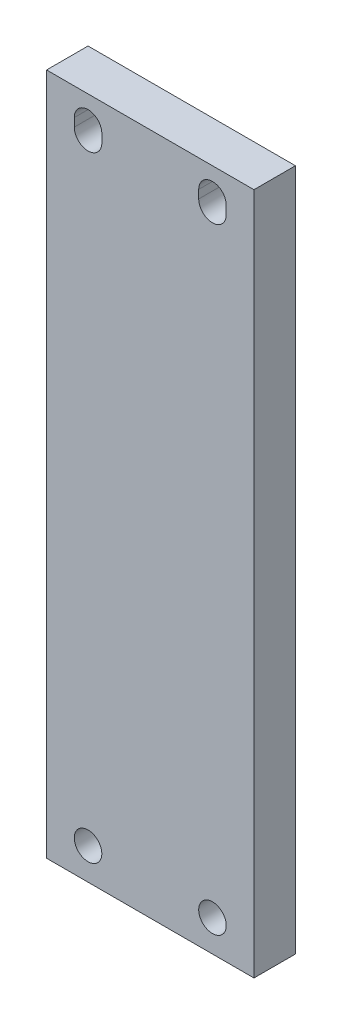
SolidWorks part; units mm, degrees
material "6061-T6 Al"
ref_plane "Front" through (0, 0, 0) normal (0, 0, 1) x (1, 0, 0)
ref_plane "Top" through (0, 0, 0) normal (0, 1, 0) x (1, 0, 0)
ref_plane "Right" through (0, 0, 0) normal (1, 0, 0) x (0, 0, -1)
sketch "Sketch1 w/mock PCB" plane through (0, 0, 0) normal (0, 0, 1) x (1, 0, 0)
  line L0 (-31.75, 104.521) -> (31.75, -104.521) construction
  line L2 (-31.75, 104.521) -> (31.75, 104.521)
  line L3 (-31.75, 104.521) -> (-31.75, -104.521)
  line L4 (-31.75, -104.521) -> (31.75, -104.521)
  line L6 (31.75, 104.521) -> (31.75, -104.521)
  point P5 (-25.908, 20.828)
  point P6 (25.908, 20.828)
  point P7 (25.908, -20.828)
  point P8 (-25.908, -20.828)
  point P63 (-25.781, -19.05)
  point P64 (25.781, -19.05)
  dimension "D1" = 63.5
  dimension "D2" = 209.042
extrude "Boss-Extrude1" add sketch "Sketch1 w/mock PCB" along normal mid plane 12.7
hole_wizard "5/16 Clearance Hole1" positions "Sketch2" profile "Sketch1" hole size "5/16" standard "ANSI Inch" end condition through all
sketch "Sketch2" plane through (0, 0, 6.35) normal (0, 0, 1) x (1, 0, 0)
  line L0 (0, -104.521) -> (0, -94.869) construction
  line L1 (-31.75, -104.521) -> (31.75, -104.521) construction
  point P0 (-19.05, -94.869)
  point P2 (19.05, -94.869)
  dimension "D1" = 38.1
  dimension "D2" = 9.652
sketch "Sketch1" plane through (-19.05, -94.869, 6.35) normal (1, 0, 0) x (0, -1, 0)
  line L0 (0, 0) -> (0, 12.7)
  line L1 (0, 12.7) -> (4.2164, 12.7)
  line L2 (4.2164, 12.7) -> (4.2164, 0)
  line L5 (4.2164, 0) -> (0, 0)
  line L11 (0, -6.35) -> (0, 107.95) construction
  dimension "Thru Hole Dia." = 8.4328
  dimension "Thru Hole Depth" = 12.7
sketch "Sketch3" plane through (0, 0, 6.35) normal (0, 0, 1) x (1, 0, 0)
  line L0 (0, 0) -> (-19.05, 0) construction
  line L2 (-19.05, 93.599) -> (-19.05, 96.139) construction
  line L3 (-23.2664, 93.599) -> (-23.2664, 96.139)
  line L4 (-14.8336, 93.599) -> (-14.8336, 96.139)
  line L5 (31.75, 104.521) -> (-31.75, 104.521) construction
  line L6 (0, 0) -> (0, 104.521) construction
  line L7 (19.05, 93.599) -> (19.05, 96.139) construction
  line L8 (23.2664, 93.599) -> (23.2664, 96.139)
  line L9 (14.8336, 93.599) -> (14.8336, 96.139)
  arc A0 (-23.2664, 93.599) -> (-14.8336, 93.599) centre (-19.05, 93.599) ccw
  arc A1 (-14.8336, 96.139) -> (-23.2664, 96.139) centre (-19.05, 96.139) ccw
  circle A2 centre (-19.05, -94.869) radius 4.2164 construction
  arc A3 (23.2664, 93.599) -> (14.8336, 93.599) centre (19.05, 93.599) cw
  arc A4 (14.8336, 96.139) -> (23.2664, 96.139) centre (19.05, 96.139) cw
  point P7 (-19.05, 94.869)
  point P22 (19.05, 94.869)
  point P27 (19.05, 94.869)
  dimension "D1" = 2.54
extrude "Cut-Extrude1" cut sketch "Sketch3" against normal through all
